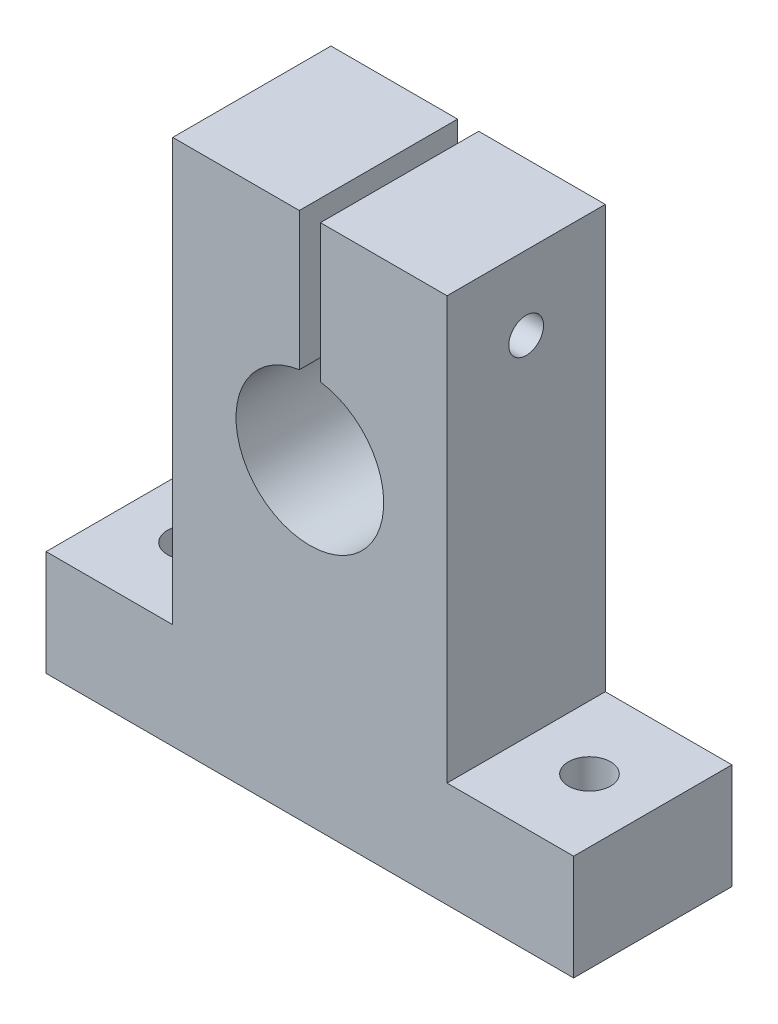
SolidWorks part; units mm, degrees
ref_plane "Front Plane" through (0, 0, 0) normal (0, 0, 1) x (1, 0, 0)
ref_plane "Top Plane" through (0, 0, 0) normal (0, 1, 0) x (1, 0, 0)
ref_plane "Right Plane" through (0, 0, 0) normal (1, 0, 0) x (0, 0, -1)
sketch "Sketch1" plane through (0, 0, 0) normal (0, 0, 1) x (1, 0, 0)
  line L1 (-26, 0) -> (-26, -40)
  line L2 (-26, -40) -> (-38, -40)
  line L3 (-38, -40) -> (-38, -50)
  line L4 (-38, -50) -> (12, -50)
  line L5 (12, -50) -> (12, -40)
  line L6 (12, -40) -> (0, -40)
  line L7 (0, -40) -> (0, 0)
  line L8 (-14, 0) -> (-14, -13.0718)
  line L9 (-12, 0) -> (-12, -13.0718)
  line L10 (-26, 0) -> (-14, 0)
  line L11 (-12, 0) -> (0, 0)
  arc A7 (-14, -13.0718) -> (-12, -13.0718) centre (-13, -20) ccw
  point P11 (0, -40)
  point P14 (-26, -40)
  point P17 (12, -40)
  point P20 (-38, -40)
  point P23 (0, 0)
  dimension "D6" = 13
  dimension "D7" = 7
  dimension "D9" = 1
  dimension "D14" = 0
  dimension "D1" = 50
  dimension "D2" = 12
  dimension "D3" = 12
  dimension "D4" = 10
  dimension "D5" = 50
  dimension "D8" = 2
  dimension "D11" = 30
  dimension "D13" = 50
extrude "Boss-Extrude1" add sketch "Sketch1" along normal blind 15
sketch "Sketch5" plane through (0, -40, 0) normal (0, 1, 0) x (1, 0, 0)
  line L0 (12, 0) -> (0, 0) construction
  line L1 (-26, 0) -> (-38, 0) construction
  line L4 (12, -15) -> (12, 0) construction
  line L5 (-38, -15) -> (-38, 0) construction
  circle A0 centre (6, -7.5) radius 2
  circle A1 centre (-32, -7.5) radius 2
  dimension "D3" = 4
  dimension "D4" = 4
  dimension "D1" = 7.5
  dimension "D2" = 7.5
  dimension "D5" = 6
  dimension "D6" = 6
extrude "Cut-Extrude3" cut sketch "Sketch5" against normal blind 15
hole_wizard "Dégagement M41" positions "Esquisse1" profile "Esquisse2" hole size "M4" standard "ISO" end condition up to next
sketch "Esquisse1" plane through (-26, 0, 0) normal (-1, 0, 0) x (0, 0, 1)
  line L0 (15, 0) -> (0, 0) construction
  point P0 (7.5699, -7)
  dimension "D1" = 7
sketch "Esquisse2" plane through (-26, -7, 7.5699) normal (0, 1, 0) x (0, 0, 1)
  line L0 (0, 0) -> (0, 12)
  line L1 (0, 12) -> (2.25, 12)
  line L2 (2.25, 12) -> (2.25, 0)
  line L5 (2.25, 0) -> (0, 0)
  line L11 (0, -6.35) -> (0, 107.95) construction
  dimension "Diamètre du perçage jusqu'au prochain" = 4.5
  dimension "Profondeur du perçage jusqu'au prochain" = 12
hole_wizard "Trou taraudé M41" positions "Esquisse3" profile "Esquisse4" tap size "M4" standard "ISO" end condition up to next
sketch "Esquisse3" plane through (0, 0, 0) normal (1, 0, 0) x (0, 0, -1)
  line L0 (-15, -40) -> (-15, 0) construction
  line L1 (-15, 0) -> (0, 0) construction
  point P0 (-7.5, -7)
  dimension "D1" = 7.5
  dimension "D2" = 7
sketch "Esquisse4" plane through (0, -7, 7.5) normal (0, 1, 0) x (0, 0, -1)
  line L0 (0, 0) -> (0, 12)
  line L1 (0, 12) -> (1.65, 12)
  line L2 (1.65, 12) -> (1.65, 0)
  line L5 (1.65, 0) -> (0, 0)
  line L11 (0, -6.35) -> (0, 107.95) construction
  dimension "Diamètre du trou pour taraudage jusqu'au prochain" = 3.3
  dimension "Profondeur du trou pour taraudage jusqu'au prochain" = 12
cosmetic thread "Filetage de perçage1" parameters "D2"=4
move or copy body "Body-Move/Copy1" [suppressed] bodies to move or copy 108
